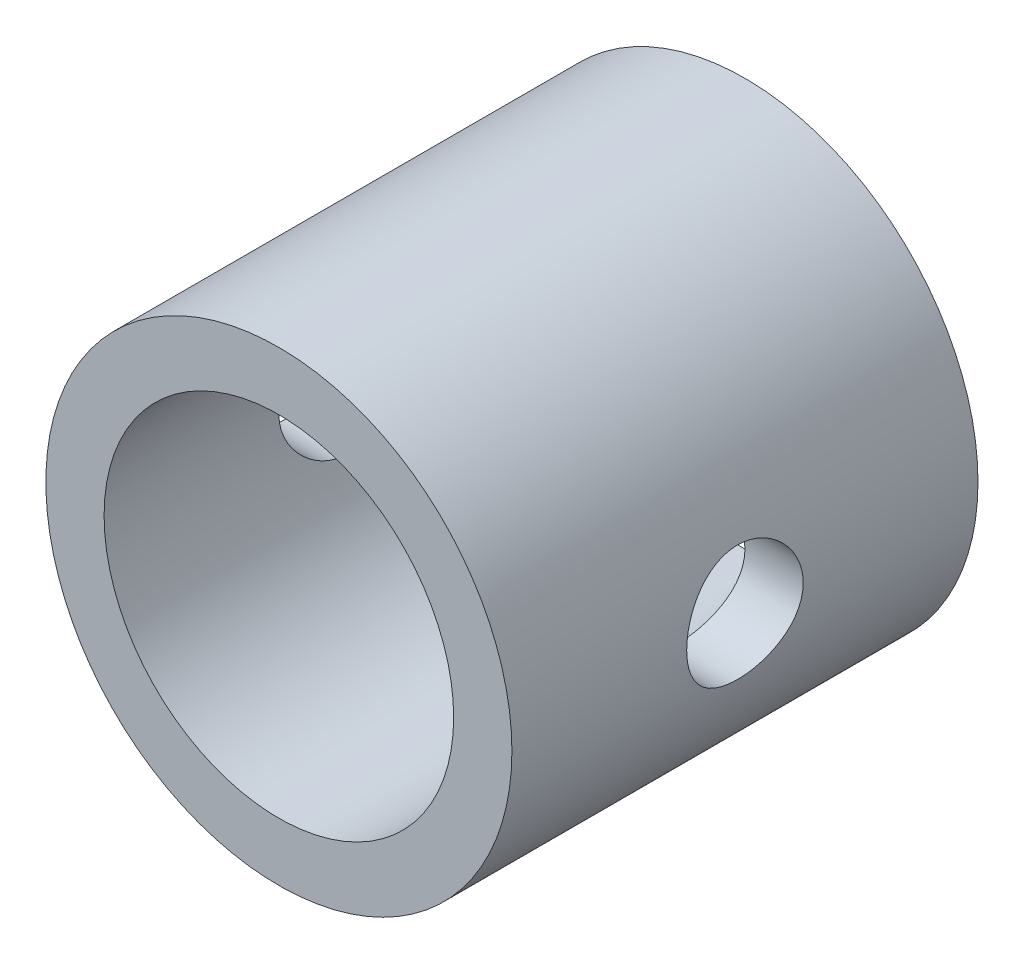
SolidWorks part; units mm, degrees
ref_plane "Front Plane" through (0, 0, 0) normal (0, 0, 1) x (1, 0, 0)
ref_plane "Top Plane" through (0, 0, 0) normal (0, 1, 0) x (1, 0, 0)
ref_plane "Right Plane" through (0, 0, 0) normal (1, 0, 0) x (0, 0, -1)
sketch "Sketch1" plane through (0, 0, 0) normal (0, 0, 1) x (1, 0, 0)
  circle A0 centre (0, 0) radius 10
  circle A1 centre (0, 0) radius 7.5
  dimension "D1" = 15
  dimension "D2" = 20
extrude "Boss-Extrude1" add sketch "Sketch1" along normal blind 20
sketch "Sketch2" plane through (0, 0, 0) normal (1, 0, 0) x (0, 0, -1)
  line L0 (-10, 10) -> (-10, -10) construction
  line L2 (-20, -10) -> (0, -10) construction
  circle A0 centre (-10, 0) radius 2.5
  dimension "D1" = 5
extrude "Cut-Extrude1" cut sketch "Sketch2" against normal through all and the other way through all
